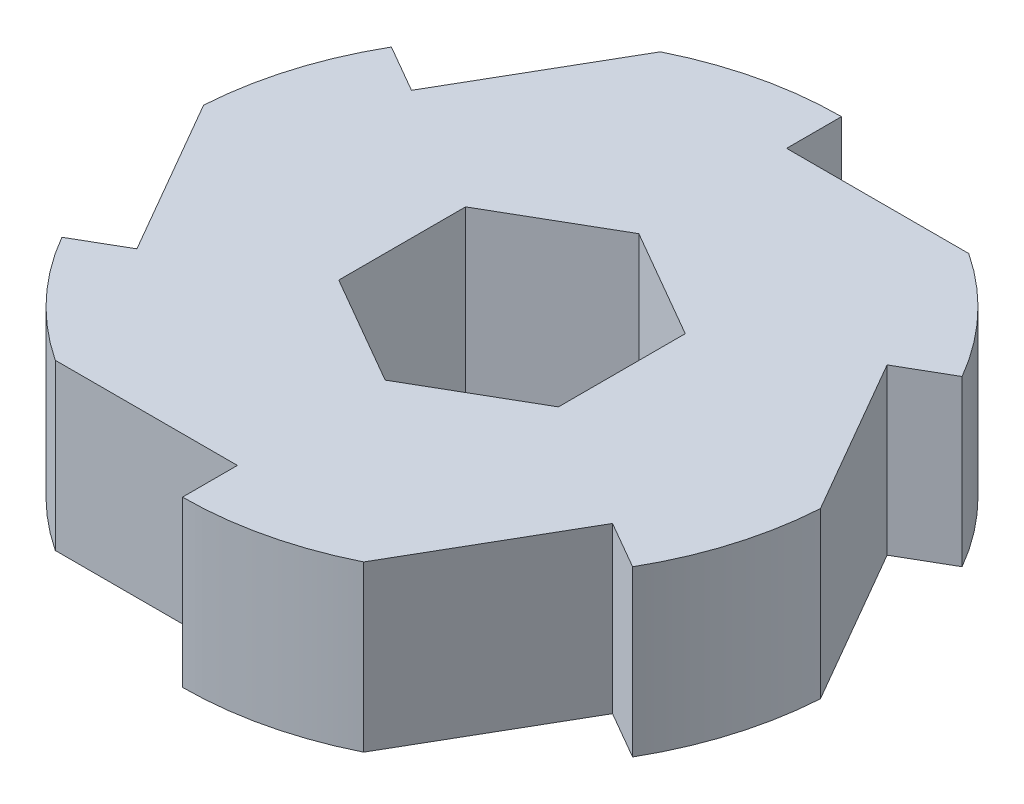
SolidWorks part; units mm, degrees
material "6061-T6 (SS)"
ref_plane "Front" through (0, 0, 0) normal (0, 0, 1) x (1, 0, 0)
ref_plane "Top" through (0, 0, 0) normal (0, 1, 0) x (1, 0, 0)
ref_plane "Right" through (0, 0, 0) normal (1, 0, 0) x (0, 0, -1)
sketch "Sketch2" plane through (0, 0, 0) normal (0, 1, 0) x (1, 0, 0)
  circle A0 centre (0, 0) radius 19.05
  dimension "D1" = 38.1
extrude "Boss-Extrude2" add sketch "Sketch2" along normal blind 9.525
sketch "Sketch3" plane through (0, 9.525, 0) normal (0, 1, 0) x (1, 0, 0)
  line L0 (0, 19.05) -> (0, 15.875)
  line L1 (0, 15.875) -> (10.5303, 15.875)
  circle A0 centre (0, 0) radius 19.05 construction
  dimension "D1" = 3.175
extrude "Cut-Extrude1" cut sketch "Sketch3" against normal through all and the other way through all
pattern_circular "CirPattern1" count 6 over 360 about axis through (0, 9.525, 0) along (0, -1, 0) of "Cut-Extrude1"
sketch "Sketch4" plane through (0, 9.525, 0) normal (0, 1, 0) x (1, 0, 0)
  line L7 (0, 7.3323) -> (-6.35, 3.6662)
  line L8 (-6.35, 3.6662) -> (-6.35, -3.6662)
  line L9 (-6.35, -3.6662) -> (0, -7.3323)
  line L10 (0, -7.3323) -> (6.35, -3.6662)
  line L11 (6.35, -3.6662) -> (6.35, 3.6662)
  line L12 (6.35, 3.6662) -> (0, 7.3323)
  circle A0 centre (0, 0) radius 6.35 construction
  point P1 (6.4133, 3.5543)
  point P10 (6.35, 0)
  dimension "D1" = 12.7
extrude "Cut-Extrude2" cut sketch "Sketch4" against normal through all
